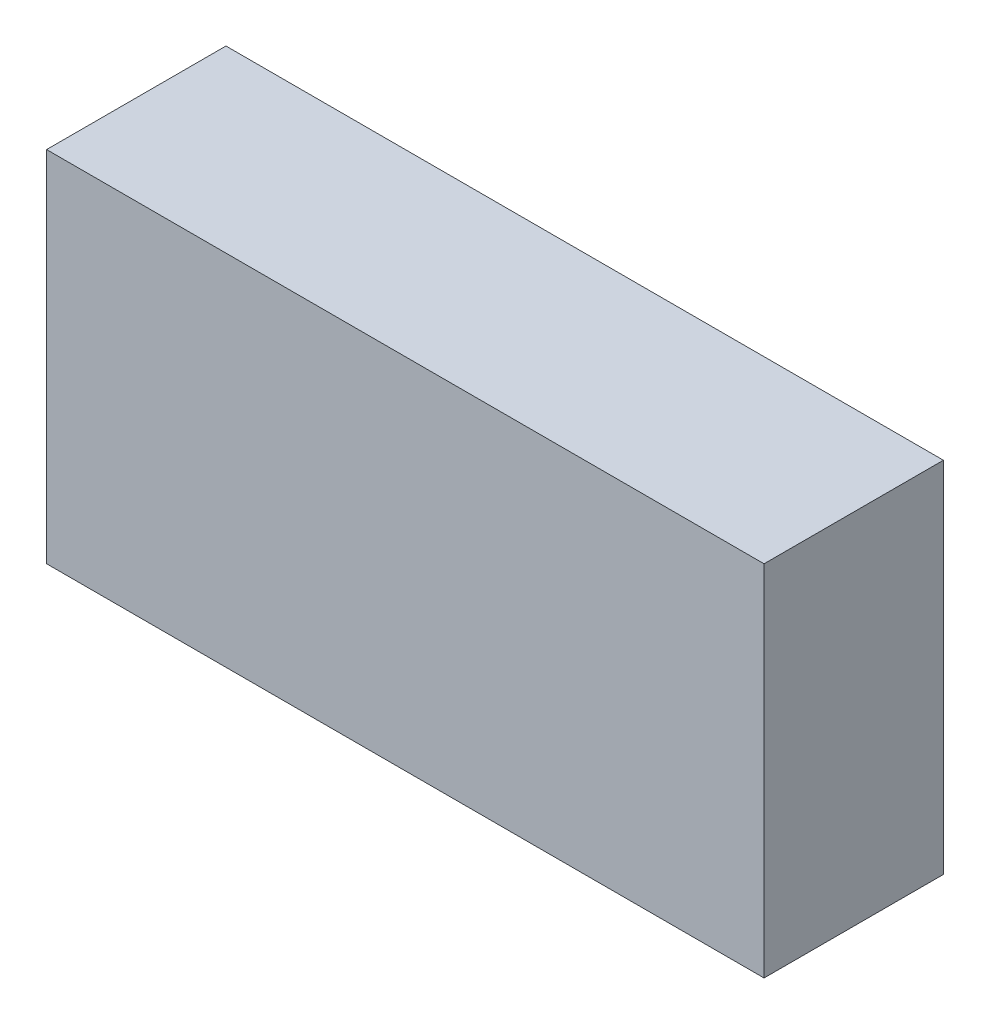
SolidWorks part; units mm, degrees
ref_plane "Front Plane" through (0, 0, 0) normal (0, 0, 1) x (1, 0, 0)
ref_plane "Top Plane" through (0, 0, 0) normal (0, 1, 0) x (1, 0, 0)
ref_plane "Right Plane" through (0, 0, 0) normal (1, 0, 0) x (0, 0, -1)
sketch "Sketch1" plane through (0, 0, 0) normal (0, 1, 0) x (1, 0, 0)
  line L1 (-42.151, 67.2187) -> (59.449, 67.2187)
  line L2 (-42.151, 67.2187) -> (-42.151, 41.8187)
  line L3 (-42.151, 41.8187) -> (59.449, 41.8187)
  line L4 (59.449, 67.2187) -> (59.449, 41.8187)
  dimension "D1" = 101.6
  dimension "D2" = 25.4
extrude "Boss-Extrude1" add sketch "Sketch1" along normal blind 50.8
